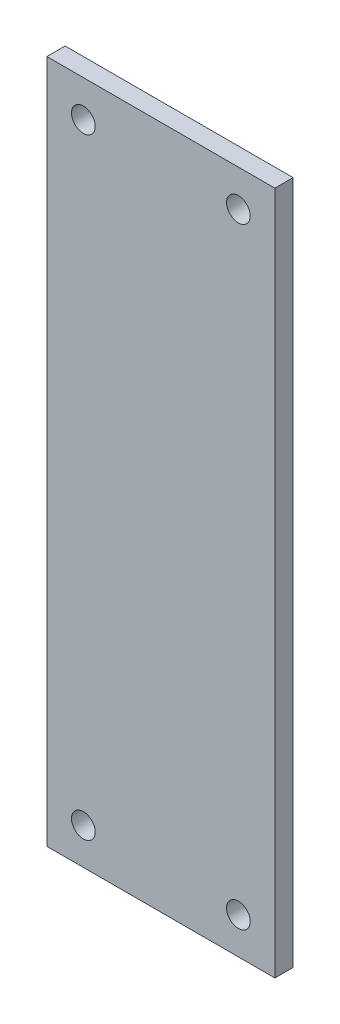
SolidWorks part; units mm, degrees
ref_plane "Спереди" through (0, 0, 0) normal (0, 0, 1) x (1, 0, 0)
ref_plane "Сверху" through (0, 0, 0) normal (0, 1, 0) x (1, 0, 0)
ref_plane "Справа" through (0, 0, 0) normal (1, 0, 0) x (0, 0, -1)
sketch "Эскиз1" plane through (0, 0, 0) normal (0, 0, 1) x (1, 0, 0)
  line L0 (125, -375) -> (125, 375)
  line L1 (125, 375) -> (-125, 375)
  line L2 (-125, 375) -> (-125, -375)
  line L3 (-125, -375) -> (125, -375)
  circle A0 centre (-85, -335) radius 13
  circle A1 centre (85, -335) radius 13
  circle A4 centre (-85, 335) radius 13
  circle A5 centre (85, 335) radius 13
extrude "Бобышка-Вытянуть1" add sketch "Эскиз1" along normal blind 20
